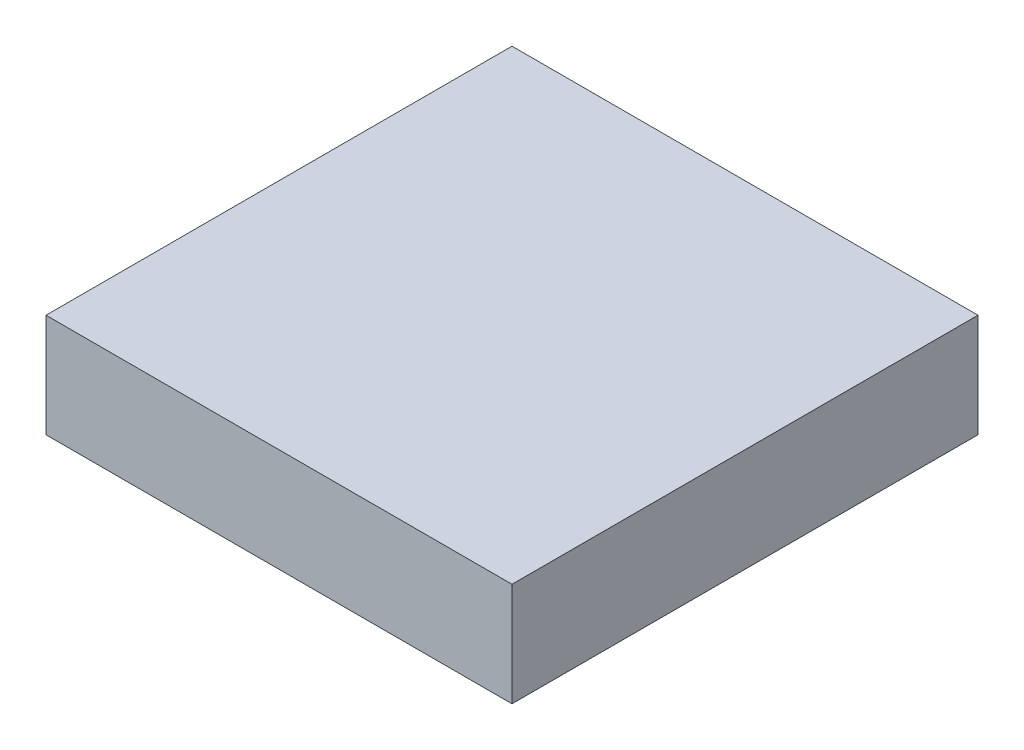
SolidWorks part; units mm, degrees
ref_plane "Front Plane" through (0, 0, 0) normal (0, 0, 1) x (1, 0, 0)
ref_plane "Top Plane" through (0, 0, 0) normal (0, 1, 0) x (1, 0, 0)
ref_plane "Right Plane" through (0, 0, 0) normal (1, 0, 0) x (0, 0, -1)
sketch "Sketch1" plane through (0, 0, 0) normal (0, 1, 0) x (1, 0, 0)
  line L1 (-22.5, 22.5) -> (22.5, 22.5)
  line L2 (-22.5, 22.5) -> (-22.5, -22.5)
  line L3 (-22.5, -22.5) -> (22.5, -22.5)
  line L4 (22.5, 22.5) -> (22.5, -22.5)
  line L5 (-22.5, 22.5) -> (22.5, -22.5) construction
  line L6 (-22.5, -22.5) -> (22.5, 22.5) construction
  point P0 (0, 0)
  dimension "D1" = 45
  dimension "D2" = 45
extrude "Boss-Extrude1" add sketch "Sketch1" along normal blind 10
